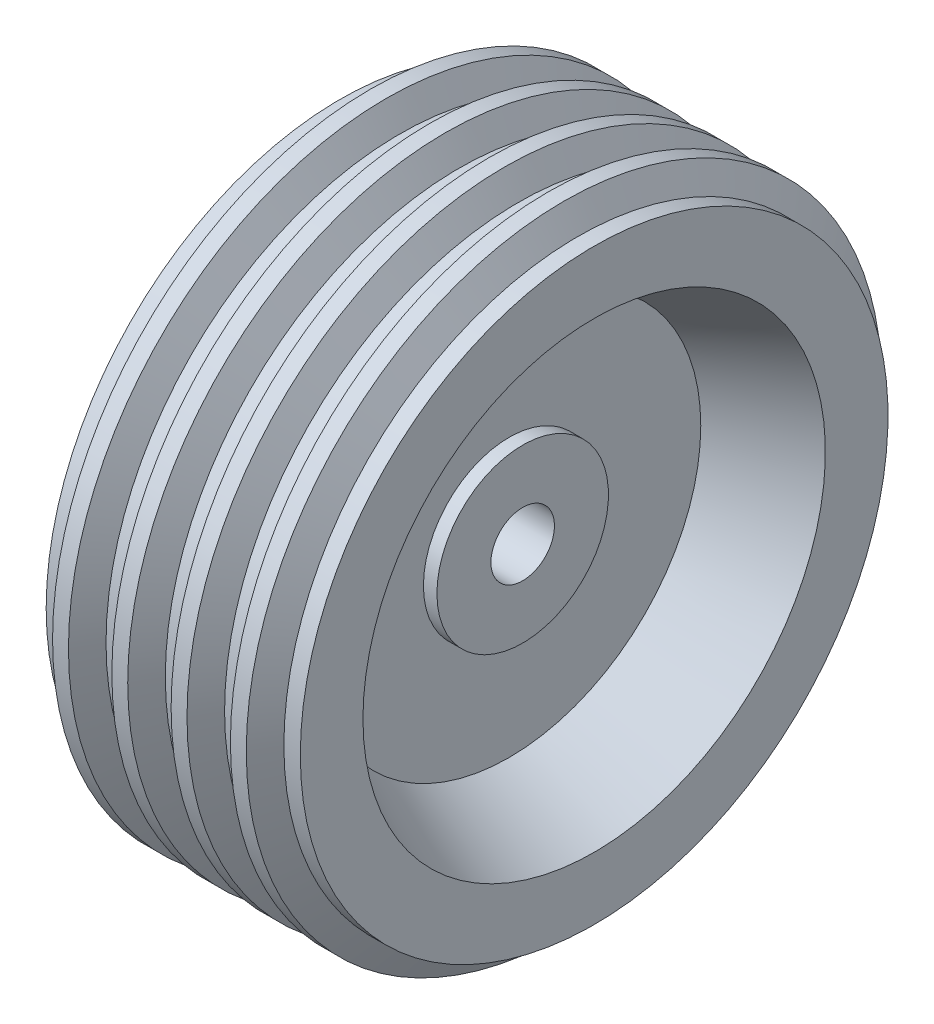
SolidWorks part; units mm, degrees
material "Gray Cast Iron"
ref_plane "Front Plane" through (0, 0, 0) normal (0, 0, 1) x (1, 0, 0)
ref_plane "Top Plane" through (0, 0, 0) normal (0, 1, 0) x (1, 0, 0)
ref_plane "Right Plane" through (0, 0, 0) normal (1, 0, 0) x (0, 0, -1)
sketch "Sketch2" plane through (0, 0, 0) normal (0, 0, 1) x (1, 0, 0)
  line L0 (-192.5707, 0) -> (195.3117, 0) construction
  line L1 (-35, 20) -> (35, 20)
  line L2 (0, 0) -> (0, 216.2431) construction
  line L3 (-35, 20) -> (-35, 54)
  line L4 (-5, 185) -> (5, 185)
  line L5 (-80, 185) -> (-69.641, 185)
  line L6 (-80, 185) -> (-80, 145.57)
  line L7 (-80, 145.57) -> (-26.5, 120.6225)
  line L8 (-26.5, 120.6225) -> (-26.5, 54)
  line L9 (-35, 54) -> (-26.5, 54)
  line L11 (-5, 185) -> (-13.6603, 200)
  line L12 (-13.6603, 200) -> (-23.6603, 200)
  line L13 (42.3205, 185) -> (32.3205, 185)
  line L14 (-23.6603, 200) -> (-32.3205, 185)
  line L15 (-32.3205, 185) -> (-42.3205, 185)
  line L16 (50.9808, 200) -> (42.3205, 185)
  line L17 (-69.641, 185) -> (-60.9808, 200)
  line L18 (-60.9808, 200) -> (-50.9808, 200)
  line L19 (-50.9808, 200) -> (-42.3205, 185)
  line L20 (-42.3205, 185) -> (-32.3205, 185)
  line L22 (60.9808, 200) -> (50.9808, 200)
  line L23 (69.641, 185) -> (60.9808, 200)
  line L24 (32.3205, 185) -> (42.3205, 185)
  line L25 (23.6603, 200) -> (32.3205, 185)
  line L26 (13.6603, 200) -> (23.6603, 200)
  line L27 (5, 185) -> (13.6603, 200)
  line L28 (35, 54) -> (26.5, 54)
  line L29 (26.5, 120.6225) -> (26.5, 54)
  line L30 (80, 145.57) -> (26.5, 120.6225)
  line L31 (80, 185) -> (80, 145.57)
  line L32 (80, 185) -> (69.641, 185)
  line L33 (35, 20) -> (35, 54)
  point P34 (0, 185)
  point P35 (0, 20)
  dimension "D2" = 10
  dimension "D3" = 34
  dimension "D4" = 54.43
  dimension "D5" = 35
  dimension "D6" = 39.43
  dimension "D7" = 115
  dimension "D8" = 120
  dimension "D9" = 10
  dimension "D10" = 120
  dimension "D11" = 10
  dimension "D12" = 120
  dimension "D13" = 5
  dimension "D14" = 120
  dimension "D15" = 8.5
  dimension "D16" = 53
  dimension "D17" = 160
  dimension "D18" = 20
revolve "Revolve1" add sketch "Sketch2" angle 360 about L0
